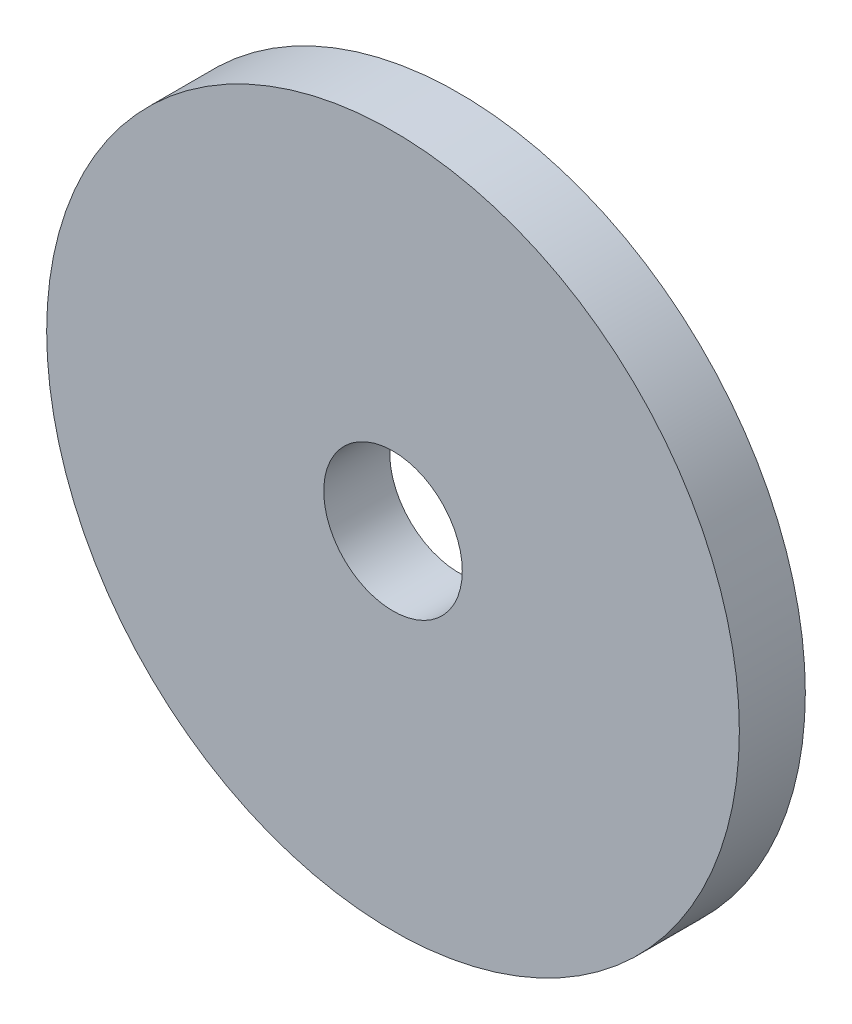
SolidWorks part; units mm, degrees
material "Stainless Steel (ferritic)"
ref_plane "Plan de face" through (0, 0, 0) normal (0, 0, 1) x (1, 0, 0)
ref_plane "Plan de dessus" through (0, 0, 0) normal (0, 1, 0) x (1, 0, 0)
ref_plane "Plan de droite" through (0, 0, 0) normal (1, 0, 0) x (0, 0, -1)
sketch "Sketch1" plane through (0, 0, 0) normal (0, 0, 1) x (1, 0, 0)
  circle A0 centre (0, 0) radius 2.1
  circle A1 centre (0, 0) radius 10.5
  dimension "D1" = 4.2
  dimension "D2" = 21
extrude "Boss-Extrude1" add sketch "Sketch1" along normal blind 2
